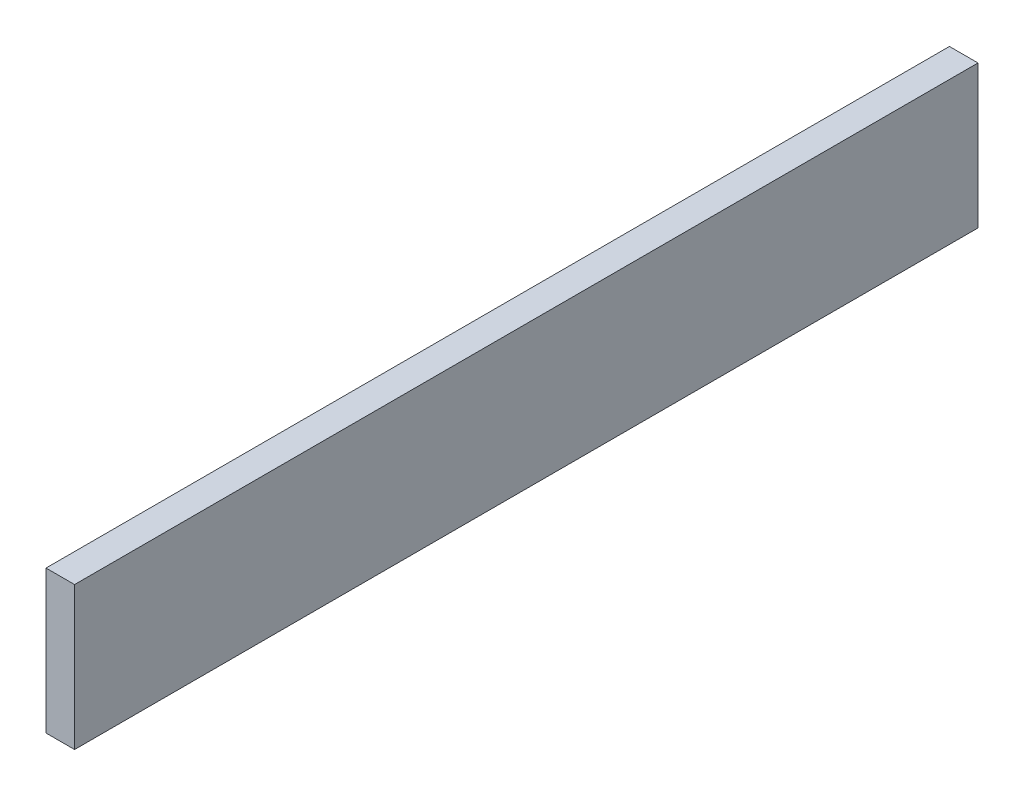
SolidWorks part; units mm, degrees
material "Силиконовая резина"
ref_plane "Спереди" through (0, 0, 0) normal (0, 0, 1) x (1, 0, 0)
ref_plane "Сверху" through (0, 0, 0) normal (0, 1, 0) x (1, 0, 0)
ref_plane "Справа" through (0, 0, 0) normal (1, 0, 0) x (0, 0, -1)
sketch "Эскиз1" plane through (0, 0, 0) normal (1, 0, 0) x (0, 0, -1)
  line L1 (0, 0) -> (31.61, 0)
  line L2 (0, 0) -> (0, 5)
  line L3 (0, 5) -> (31.61, 5)
  line L4 (31.61, 0) -> (31.61, 5)
  dimension "D1" = 31.61
  dimension "D2" = 5
extrude "Бобышка-Вытянуть1" add sketch "Эскиз1" along normal blind 1
